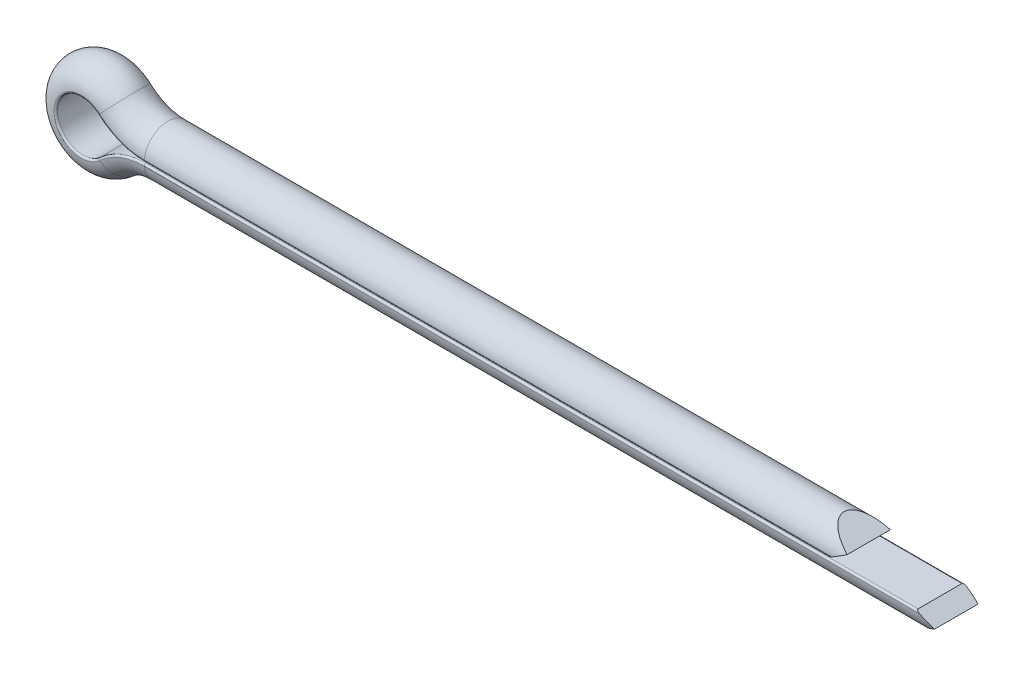
SolidWorks part; units mm, degrees
material "220M07"
ref_plane "Front Plane" through (0, 0, 0) normal (0, 0, 1) x (1, 0, 0)
ref_plane "Top Plane" through (0, 0, 0) normal (0, 1, 0) x (1, 0, 0)
ref_plane "Right Plane" through (0, 0, 0) normal (1, 0, 0) x (0, 0, -1)
sketch "Sketch1" plane through (0, 0, 0) normal (0, 0, 1) x (1, 0, 0)
  line L0 (21.8, 0.7) -> (1.8, 0.7)
  line L1 (1.8, -0.7) -> (24.3, -0.7)
  line L2 (0, 0) -> (54.6273, 0) construction
  line L3 (0, 0) -> (-1.4, 0) construction
  arc A0 (1.8, 0.7) -> (0.9458, 1.0322) centre (1.8, 1.9643) cw
  arc A1 (0.9458, 1.0322) -> (0.9458, -1.0322) centre (0, 0) ccw
  arc A2 (0.9458, -1.0322) -> (1.8, -0.7) centre (1.8, -1.9643) cw
  dimension "D1" = 1.4
  dimension "head-dia" = 2.8
  dimension "D3" = 3.2
  dimension "D4" = 20
  dimension "extended-length" = 2.5
ref_plane "Plane1" through (21.8, 0, 0) normal (1, 0, 0) x (0, 0, -1)
sketch "Sketch2" plane through (21.8, 0, 0) normal (1, 0, 0) x (0, 0, -1)
  line L0 (0, 1.4) -> (0, -1.4) construction
  line L1 (0.675, 0.025) -> (-0.675, 0.025)
  arc A0 (-0.675, 0.025) -> (0.675, 0.025) centre (0, 0.025) cw
  dimension "D1" = 1.35
sweep "Sweep1" add profiles "Sketch2" path "Sketch1"
sketch "Sketch3" plane through (0, 0, 0) normal (0, 0, 1) x (1, 0, 0)
  line L0 (21.3323, 0.025) -> (21.8, 0.295)
  line L1 (21.8, 0.025) -> (1.8, 0.025) construction
  line L2 (21.8, -0.4638) -> (21.8, 0.4638) construction
  line L3 (21.8, 0.295) -> (21.0985, 0.7)
  line L4 (21.8, 0.7) -> (1.8, 0.7) construction
  line L5 (21.0985, 0.7) -> (25.3, 0.7)
  line L6 (25.3, 0.7) -> (25.3, -0.7)
  line L7 (25.3, -0.7) -> (23.5985, -0.7)
  line L8 (23.5985, -0.7) -> (24.3, -0.295)
  line L9 (24.3, -0.7) -> (24.3, -0.025) construction
  line L10 (24.3, -0.295) -> (23.8323, -0.025)
  line L11 (1.8, -0.025) -> (24.3, -0.025) construction
  line L12 (23.8323, -0.025) -> (21.8, -0.025)
  line L14 (1.8, -0.7) -> (24.3, -0.7) construction
  line L15 (21.8, 0.7) -> (21.8, 0.295) construction
  line L16 (21.8, 0.295) -> (21.8, -0.025) construction
  line L17 (21.8, -0.025) -> (21.8, 0.025)
  line L18 (21.8, 0.025) -> (21.3323, 0.025)
  dimension "D1" = 60
  dimension "D2" = 30
  dimension "D3" = 30
  dimension "D4" = 60
  dimension "D5" = 0.405
  dimension "D6" = 0.405
  dimension "D7" = 1
extrude "Cut-Extrude1" cut sketch "Sketch3" against normal through all both and the other way through all
fillet "Fillet1" radius 0.05 10 edges at (12.8162, -0.025, 0.675) (12.8162, -0.025, -0.675) (1.0971, -0.1569, -0.675) (1.0971, -0.1569, 0.675) (-0.725, 0, -0.675) (-0.725, 0, 0.675) (1.0971, 0.1569, -0.675) (1.0971, 0.1569, 0.675) (11.5662, 0.025, -0.675) (11.5662, 0.025, 0.675)
